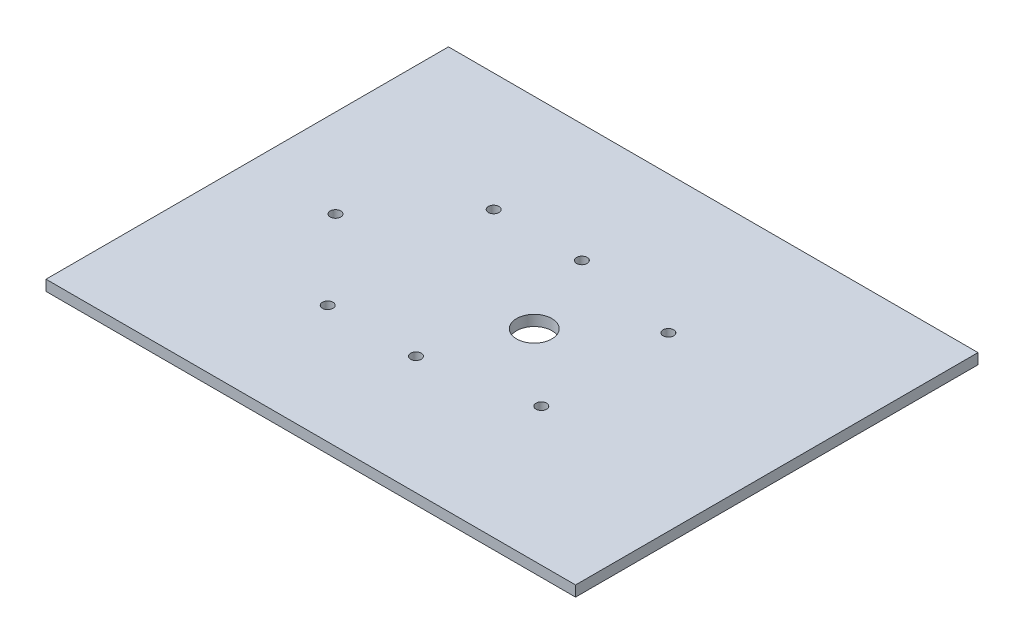
SolidWorks part; units mm, degrees
ref_plane "前视基准面" through (0, 0, 0) normal (0, 0, 1) x (1, 0, 0)
ref_plane "上视基准面" through (0, 0, 0) normal (0, 1, 0) x (1, 0, 0)
ref_plane "右视基准面" through (0, 0, 0) normal (1, 0, 0) x (0, 0, -1)
sketch "草图1" plane through (0, 0, 0) normal (0, 1, 0) x (1, 0, 0)
  line L0 (0, 0) -> (150, 0)
  line L1 (150, 0) -> (150, -114)
  line L2 (150, -114) -> (0, -114)
  line L3 (0, -114) -> (0, 0)
extrude "凸台-拉伸1" add sketch "草图1" along normal blind 3
sketch "草图2" plane through (0, 3, 0) normal (0, 1, 0) x (1, 0, 0)
  line L0 (-150, -57) -> (150, -57) construction
  line L1 (0, 0) -> (0, -114) construction
  line L2 (150, -114) -> (150, 0) construction
  circle A0 centre (25, -57) radius 1.5
  circle A1 centre (101.3, -75) radius 1.5
  circle A2 centre (101.3, -39) radius 1.5
  circle A3 centre (71.3, -80.5) radius 1.5
  circle A4 centre (46.3, -80.5) radius 1.5
  circle A5 centre (71.3, -33.5) radius 1.5
  circle A6 centre (46.3, -33.5) radius 1.5
  circle A7 centre (81.3, -57) radius 5
  point P17 (0, -57)
  dimension "D1" = 36
  dimension "D3" = 47
  dimension "D6" = 30
  dimension "D7" = 20
  dimension "D2" = 76.3
  dimension "D4" = 25
  dimension "D5" = 25
extrude "切除-拉伸1" cut sketch "草图2" against normal blind 3
